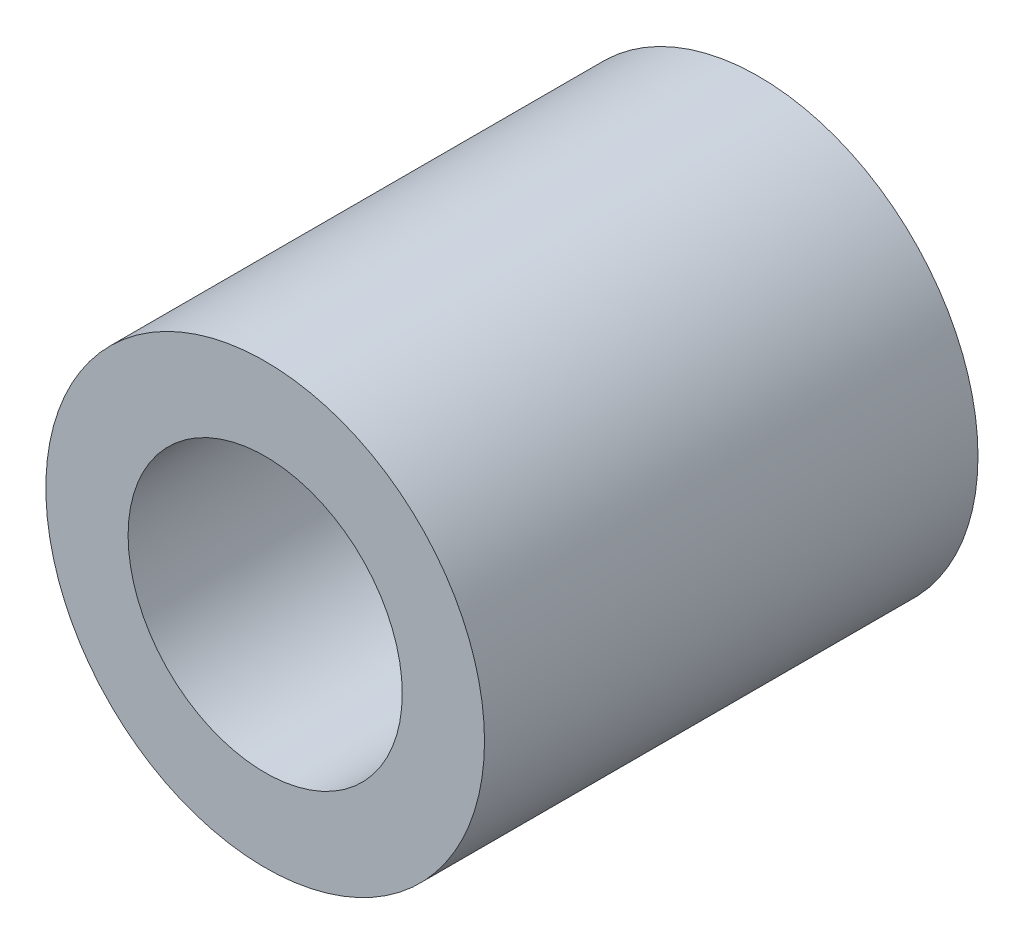
SolidWorks part; units mm, degrees
ref_plane "Alzado" through (0, 0, 0) normal (0, 0, 1) x (1, 0, 0)
ref_plane "Planta" through (0, 0, 0) normal (0, 1, 0) x (1, 0, 0)
ref_plane "Vista lateral" through (0, 0, 0) normal (1, 0, 0) x (0, 0, -1)
sketch "Croquis1" plane through (0, 0, 0) normal (0, 0, 1) x (1, 0, 0)
  circle A0 centre (0, 0) radius 5
  circle A1 centre (0, 0) radius 8
  dimension "10" = 10
  dimension "3" = 3
extrude "Saliente-Extruir1" add sketch "Croquis1" along normal blind 18
